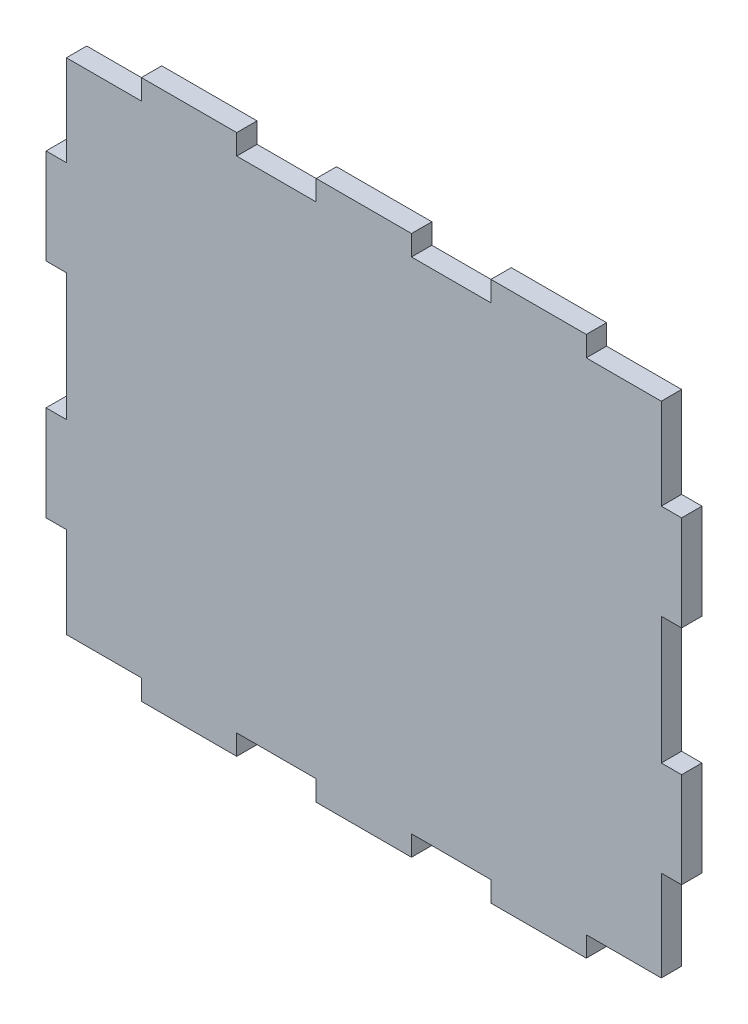
SolidWorks part; units mm, degrees
ref_plane "Front Plane" through (0, 0, 0) normal (0, 0, 1) x (1, 0, 0)
ref_plane "Top Plane" through (0, 0, 0) normal (0, 1, 0) x (1, 0, 0)
ref_plane "Right Plane" through (0, 0, 0) normal (1, 0, 0) x (0, 0, -1)
sketch "Sketch1" plane through (0, 0, 0) normal (0, 0, 1) x (1, 0, 0)
  line L0 (-50, 10) -> (-50, 25)
  line L1 (-7.5, 42.5) -> (7.5, 42.5)
  line L2 (-46.8, 39.3) -> (-46.8, 25)
  line L3 (-46.8, 25) -> (-50, 25)
  line L4 (-50, 10) -> (-46.8, 10)
  line L5 (0, -55) -> (0, 55) construction
  line L6 (-46.8, 39.3) -> (-35, 39.3)
  line L7 (-35, 39.3) -> (-35, 42.5)
  line L8 (-20, 42.5) -> (-20, 39.3)
  line L9 (-20, 39.3) -> (-7.5, 39.3)
  line L10 (-7.5, 39.3) -> (-7.5, 42.5)
  line L11 (-46.8, 10) -> (-46.8, -10)
  line L12 (-35, 42.5) -> (-20, 42.5)
  line L13 (55, 0) -> (-55, 0) construction
  line L14 (0, 42.5) -> (0, -42.5) construction
  line L15 (46.8, 0) -> (-46.8, 0) construction
  line L16 (35, 42.5) -> (20, 42.5)
  line L17 (46.8, 10) -> (46.8, -10)
  line L18 (7.5, 39.3) -> (7.5, 42.5)
  line L19 (20, 39.3) -> (7.5, 39.3)
  line L20 (20, 42.5) -> (20, 39.3)
  line L21 (35, 39.3) -> (35, 42.5)
  line L22 (46.8, 39.3) -> (35, 39.3)
  line L23 (50, 10) -> (46.8, 10)
  line L24 (46.8, 25) -> (50, 25)
  line L25 (46.8, 39.3) -> (46.8, 25)
  line L26 (50, 10) -> (50, 25)
  line L27 (50, -10) -> (50, -25)
  line L28 (46.8, -39.3) -> (46.8, -25)
  line L29 (46.8, -25) -> (50, -25)
  line L30 (50, -10) -> (46.8, -10)
  line L31 (46.8, -39.3) -> (35, -39.3)
  line L32 (35, -39.3) -> (35, -42.5)
  line L33 (20, -42.5) -> (20, -39.3)
  line L34 (20, -39.3) -> (7.5, -39.3)
  line L35 (7.5, -39.3) -> (7.5, -42.5)
  line L36 (35, -42.5) -> (20, -42.5)
  line L37 (-35, -42.5) -> (-20, -42.5)
  line L38 (-7.5, -39.3) -> (-7.5, -42.5)
  line L39 (-20, -39.3) -> (-7.5, -39.3)
  line L40 (-20, -42.5) -> (-20, -39.3)
  line L41 (-35, -39.3) -> (-35, -42.5)
  line L42 (-46.8, -39.3) -> (-35, -39.3)
  line L43 (-50, -10) -> (-46.8, -10)
  line L44 (-46.8, -25) -> (-50, -25)
  line L45 (-46.8, -39.3) -> (-46.8, -25)
  line L46 (-7.5, -42.5) -> (7.5, -42.5)
  line L47 (-50, -10) -> (-50, -25)
  dimension "D5" = 10
  dimension "D7" = 12.5
  dimension "D1" = 15
  dimension "D2" = 3.2
  dimension "D3" = 15
  dimension "D4" = 15
  dimension "D6" = 7.5
  dimension "D8" = 42.5
extrude "Boss-Extrude1" add sketch "Sketch1" along normal blind 3.2
